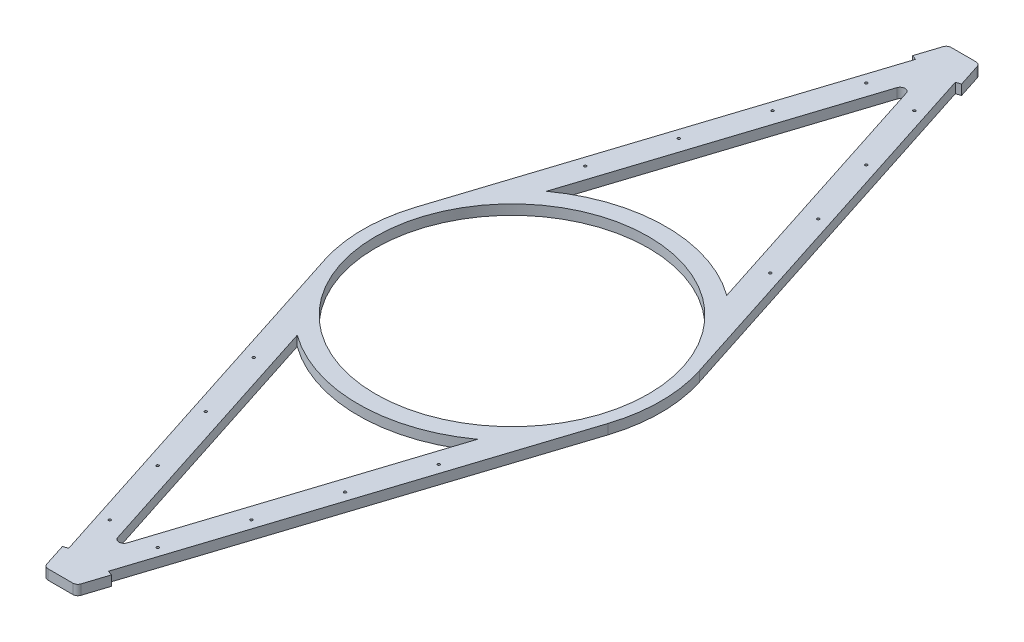
SolidWorks part; units mm, degrees
ref_plane "Front Plane" through (0, 0, 0) normal (0, 0, 1) x (1, 0, 0)
ref_plane "Top Plane" through (0, 0, 0) normal (0, 1, 0) x (1, 0, 0)
ref_plane "Right Plane" through (0, 0, 0) normal (1, 0, 0) x (0, 0, -1)
sketch "Sketch2" plane through (0, 0, 0) normal (0, 1, 0) x (1, 0, 0)
  line L0 (-295.0403, 95.1378) -> (-34.5174, 903.069)
  line L1 (-25, 910) -> (25, 910)
  line L2 (0, 0) -> (0, 979.251) construction
  line L3 (-181.6808, 251.1814) -> (-9.5174, 785.0928)
  line L4 (295.0403, 95.1378) -> (32.2825, 910)
  line L5 (181.6808, 251.1814) -> (9.5174, 785.0928)
  line L6 (0, 912.3611) -> (-253.9796, 124.7221) construction
  line L7 (0, 912.3611) -> (253.9796, 124.7221) construction
  line L8 (-638.4186, 0) -> (595.6196, 0) construction
  line L9 (181.6808, -251.1814) -> (9.5174, -785.0928)
  line L10 (295.0403, -95.1378) -> (32.2825, -910)
  line L11 (-181.6808, -251.1814) -> (-9.5174, -785.0928)
  line L12 (-25, -910) -> (25, -910)
  line L13 (-295.0403, -95.1378) -> (-34.5174, -903.069)
  circle A0 centre (0, 0) radius 250 construction
  arc A1 (181.6808, 251.1814) -> (-181.6808, 251.1814) centre (0, 0) ccw
  arc A2 (-9.5174, 785.0928) -> (9.5174, 785.0928) centre (0, 782.0238) cw
  arc A3 (-295.0403, 95.1378) -> (-295.0403, -95.1378) centre (0, 0) ccw
  arc A4 (-25, 910) -> (-34.5174, 903.069) centre (-25, 900) ccw
  arc A5 (25, 910) -> (34.5174, 903.069) centre (25, 900) cw
  circle A6 centre (-186.4767, 334.0614) radius 2.5
  circle A7 centre (-140.4423, 476.8229) radius 2.5
  circle A8 centre (-94.4079, 619.5843) radius 2.5
  circle A9 centre (-48.3735, 762.3458) radius 2.5
  circle A10 centre (48.3735, 762.3458) radius 2.5
  circle A11 centre (94.4079, 619.5843) radius 2.5
  circle A12 centre (140.4423, 476.8229) radius 2.5
  circle A13 centre (186.4767, 334.0614) radius 2.5
  circle A14 centre (0, 0) radius 275
  circle A15 centre (186.4767, -334.0614) radius 2.5
  circle A16 centre (140.4423, -476.8229) radius 2.5
  circle A17 centre (94.4079, -619.5843) radius 2.5
  circle A18 centre (48.3735, -762.3458) radius 2.5
  circle A19 centre (-48.3735, -762.3458) radius 2.5
  circle A20 centre (-94.4079, -619.5843) radius 2.5
  circle A21 centre (-140.4423, -476.8229) radius 2.5
  circle A22 centre (-186.4767, -334.0614) radius 2.5
  arc A23 (25, -910) -> (34.5174, -903.069) centre (25, -900) ccw
  arc A24 (-25, -910) -> (-34.5174, -903.069) centre (-25, -900) cw
  arc A25 (-9.5174, -785.0928) -> (9.5174, -785.0928) centre (0, -782.0238) ccw
  arc A26 (181.6808, -251.1814) -> (-181.6808, -251.1814) centre (0, 0) cw
  arc A27 (-181.6808, -251.1814) -> (181.6808, -251.1814) centre (0, 0) ccw
  arc A28 (295.0403, -95.1378) -> (295.0403, 95.1378) centre (0, 0) ccw
  point P15 (0, 814.6081)
  point P17 (-32.2825, 910)
  point P21 (0, 910)
  point P70 (0, -910)
  dimension "D1" = 500
  dimension "D2" = 10
  dimension "D3" = 10
  dimension "D4" = 5
  dimension "D10" = 550
  dimension "D5" = 150
  dimension "D6" = 150
  dimension "D7" = 150
  dimension "D8" = 60
  dimension "D9" = 910
  dimension "D11" = 50
  dimension "D12" = 30
extrude "Boss-Extrude1" add sketch "Sketch2" along normal blind 20 contours A5 L1 A4 L0 A3 L4 A12 A10 A9 A8 A7 A6 A0 L3 A2 L5 A1 A11 A13
sketch "Sketch3" plane through (0, 20, 0) normal (0, 1, 0) x (1, 0, 0)
  line L0 (-49.5235, -856.5322) -> (-40.0061, -853.4632)
  line L1 (-295.0403, -95.1378) -> (-34.5174, -903.069) construction
  line L2 (-40.0061, -853.4632) -> (-285.5229, -92.0688)
  line L3 (-49.5235, -856.5322) -> (-295.0403, -95.1378)
  line L4 (-529.7758, 0) -> (513.6799, 0) construction
  line L5 (-49.5235, 856.5322) -> (-295.0403, 95.1378)
  line L6 (-40.0061, 853.4632) -> (-285.5229, 92.0688)
  line L7 (-49.5235, 856.5322) -> (-40.0061, 853.4632)
  line L8 (49.5235, 856.5322) -> (40.0061, 853.4632)
  line L9 (40.0061, 853.4632) -> (285.5229, 92.0688)
  line L10 (49.5235, 856.5322) -> (295.0403, 95.1378)
  line L11 (49.5235, -856.5322) -> (295.0403, -95.1378)
  line L12 (40.0061, -853.4632) -> (285.5229, -92.0688)
  line L13 (49.5235, -856.5322) -> (40.0061, -853.4632)
  line L41 (0, 1098.112) -> (0, -1215.3687) construction
  arc A0 (285.5229, 92.0688) -> (285.5229, -92.0688) centre (0, 0) cw
  arc A1 (-295.0403, 95.1378) -> (-295.0403, -95.1378) centre (0, 0) ccw
  arc A2 (-285.5229, 92.0688) -> (-285.5229, -92.0688) centre (0, 0) ccw
  arc A3 (295.0403, 95.1378) -> (295.0403, -95.1378) centre (0, 0) cw
  line M26 (34.5174, -903.069) -> (295.0403, -95.1378)
  arc M27 (295.0403, -95.1378) -> (295.0403, 95.1378) centre (0, 0) ccw
  line M28 (295.0403, 95.1378) -> (34.5174, 903.069)
  line M32 (-34.5174, 903.069) -> (-295.0403, 95.1378)
  arc M33 (-295.0403, 95.1378) -> (-295.0403, -95.1378) centre (0, 0) ccw
  line M34 (-295.0403, -95.1378) -> (-34.5174, -903.069)
  dimension "D1" = 800
  dimension "D2" = 10
extrude "Cut-Extrude1" cut sketch "Sketch3" against normal through all contours A2 L6 L7 L0 L2 M32 M33 M34 | L9 A0 L12 L13 L8 M26 M27 M28
